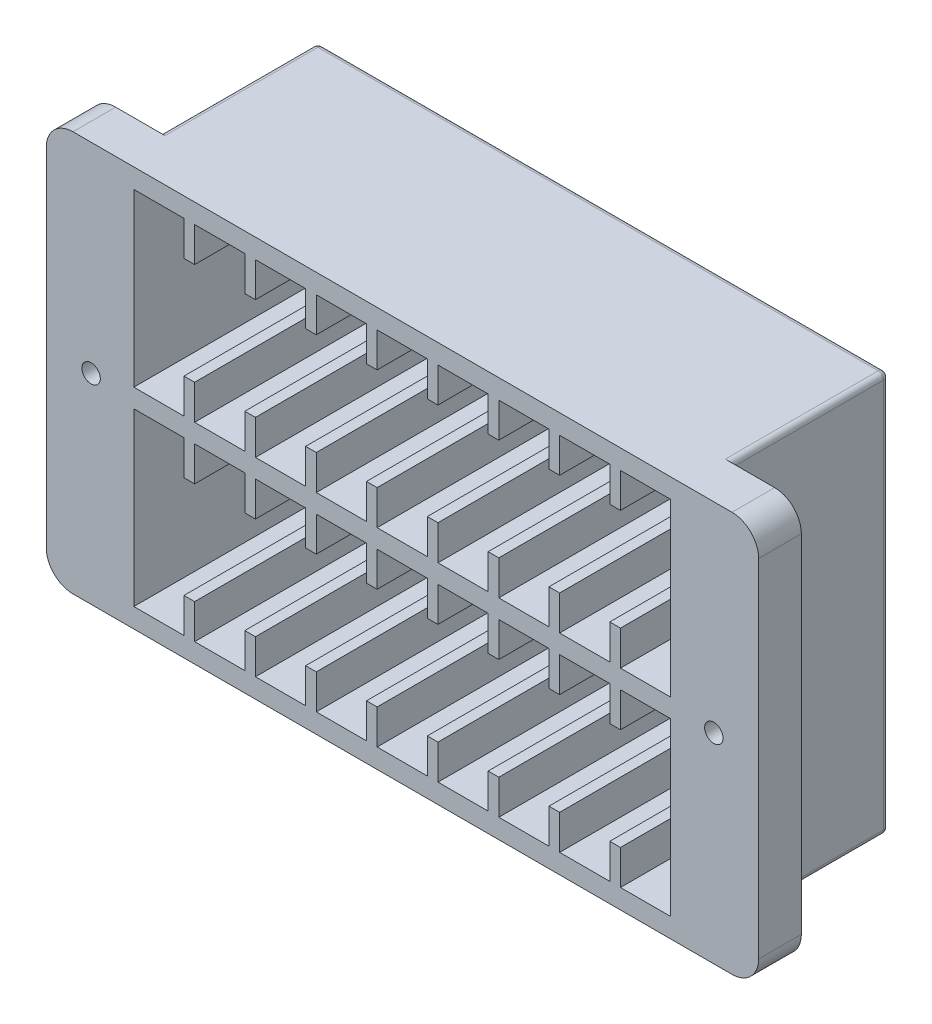
SolidWorks part; units mm, degrees
ref_plane "Front Plane" through (0, 0, 0) normal (0, 0, 1) x (1, 0, 0)
ref_plane "Top Plane" through (0, 0, 0) normal (0, 1, 0) x (1, 0, 0)
ref_plane "Right Plane" through (0, 0, 0) normal (1, 0, 0) x (0, 0, -1)
sketch "Sketch1" plane through (0, 0, 0) normal (0, 0, 1) x (1, 0, 0)
  line L0 (58.35, 0) -> (-58.35, 0) construction
  line L1 (66.75, -37.5) -> (-66.75, -37.5)
  line L2 (66.75, -37.5) -> (66.75, 37.5)
  line L3 (66.75, 37.5) -> (-66.75, 37.5)
  line L4 (-66.75, -37.5) -> (-66.75, 37.5)
  line L5 (66.75, -37.5) -> (-66.75, 37.5) construction
  line L6 (66.75, 37.5) -> (-66.75, -37.5) construction
  line L7 (-58.35, -1.725) -> (-58.35, 1.725) construction
  circle A0 centre (-58.35, 0) radius 1.725
  circle A1 centre (58.35, 0) radius 1.725
  point P0 (0, 0)
  point P9 (0, 0)
  point P24 (-58.35, 0)
  dimension "D4" = 3.45
  dimension "D1" = 133.5
  dimension "D2" = 75
  dimension "D3" = 116.7
extrude "Boss-Extrude1" add sketch "Sketch1" along normal blind 8
sketch "Sketch2" plane through (0, 0, 0) normal (0, 0, -1) x (-1, 0, 0)
  line L0 (-66.75, 37.5) -> (66.75, 37.5) construction
  line L1 (53.5, -37.5) -> (-53.5, -37.5)
  line L2 (53.5, -37.5) -> (53.5, 37.5)
  line L3 (53.5, 37.5) -> (-53.5, 37.5)
  line L4 (-53.5, -37.5) -> (-53.5, 37.5)
  line L5 (53.5, -37.5) -> (-53.5, 37.5) construction
  line L6 (53.5, 37.5) -> (-53.5, -37.5) construction
  point P0 (0, 0)
  dimension "D1" = 107
extrude "Boss-Extrude2" add sketch "Sketch2" along normal blind 29.65
sketch "Sketch3" plane through (0, 0, 8) normal (0, 0, 1) x (1, 0, 0)
  line L0 (0, -1.75) -> (0, 1.75) construction
  line L6 (48.4799, 33.85) -> (40.85, 33.85)
  line L19 (50.35, 0) -> (-50.35, 0) construction
  line L20 (-38.95, 33.85) -> (-38.95, 27.35)
  line L21 (-50.35, 33.85) -> (-40.95, 33.85)
  line L22 (-50.35, 33.85) -> (-50.35, 1.75)
  line L24 (-40.95, 33.85) -> (-40.95, 27.35)
  line L25 (-38.95, 33.85) -> (-29.55, 33.85)
  line L26 (-29.55, 33.85) -> (-29.55, 27.35)
  line L40 (-27.55, 33.85) -> (-27.55, 27.35)
  line L41 (-27.55, 33.85) -> (-18.15, 33.85)
  line L75 (-18.15, 33.85) -> (-18.15, 27.35)
  line L77 (-16.15, 33.85) -> (-16.15, 27.35)
  line L93 (-16.15, 33.85) -> (-6.75, 33.85)
  line L94 (-6.75, 33.85) -> (-6.75, 27.35)
  line L96 (-4.75, 33.85) -> (-4.75, 27.35)
  line L98 (-4.75, 33.85) -> (4.65, 33.85)
  line L99 (4.65, 33.85) -> (4.65, 27.35)
  line L101 (6.65, 33.85) -> (6.65, 27.35)
  line L102 (6.65, 33.85) -> (16.05, 33.85)
  line L103 (16.05, 33.85) -> (16.05, 27.35)
  line L105 (18.05, 33.85) -> (18.05, 27.35)
  line L106 (18.05, 33.85) -> (27.45, 33.85)
  line L107 (27.45, 33.85) -> (27.45, 27.35)
  line L109 (29.45, 33.85) -> (29.45, 27.35)
  line L110 (29.45, 33.85) -> (38.85, 33.85)
  line L111 (38.85, 33.85) -> (38.85, 27.35)
  line L113 (40.85, 33.85) -> (40.85, 27.35)
  line L114 (40.85, 33.85) -> (50.25, 33.85)
  line L115 (50.25, 33.85) -> (50.25, 1.75)
  line L118 (2.9667, -1.75) -> (-5.3771, 1.75) construction
  line L119 (3.1755, 1.75) -> (-3.1755, -1.75) construction
  line L155 (-40.95, 27.35) -> (-38.95, 27.35)
  line L165 (-50.35, 1.75) -> (-50.35, 33.85)
  line L166 (-29.55, 27.35) -> (-27.55, 27.35)
  line L167 (-18.15, 27.35) -> (-16.15, 27.35)
  line L168 (-6.75, 27.35) -> (-4.75, 27.35)
  line L169 (4.65, 27.35) -> (6.65, 27.35)
  line L170 (16.05, 27.35) -> (18.05, 27.35)
  line L171 (27.45, 27.35) -> (29.45, 27.35)
  line L173 (38.85, 27.35) -> (40.85, 27.35)
  line L174 (-50.35, 1.75) -> (50.25, 1.75)
  line L175 (-50.35, -1.75) -> (50.25, -1.75)
  line L176 (-40.95, 33.85) -> (-50.35, 33.85)
  line L177 (-29.55, 33.85) -> (-38.95, 33.85)
  line L178 (-18.15, 33.85) -> (-27.55, 33.85)
  line L179 (-6.75, 33.85) -> (-16.15, 33.85)
  line L180 (4.65, 33.85) -> (-4.75, 33.85)
  line L181 (16.05, 33.85) -> (6.65, 33.85)
  line L182 (27.45, 33.85) -> (18.05, 33.85)
  line L183 (38.85, 33.85) -> (29.45, 33.85)
  point P0 (0, 0)
  point P2 (0, 0)
  point P10 (0, 0)
  point P11 (0, 0)
  point P14 (0, 0)
  point P42 (0, 0)
  point P45 (0, 0)
  dimension "D2" = 32.1
  dimension "D3" = 9.4
  dimension "D4" = 2
  dimension "D5" = 9
  dimension "D7" = 6.5
  dimension "D6" = 50.35
  dimension "D15" = 3.5
  dimension "D18" = 100.7
extrude "Cut-Extrude1" cut sketch "Sketch3" against normal blind 32.65 contours L22 L174 L115 L6 L113 L173 L111 L110 L109 L171 L107 L106 L105 L170 L103 L102 L101 L169 L99 L98 L96 L168 L94 L93 L77 L167 L75 L41 L40 L166 L26 L25 L20 L155 L24 L21
mirror "Mirror1" about plane through (0, 0, 0) normal (0, 1, 0) of "Cut-Extrude1"
sketch "Sketch4" plane through (0, 0, 8) normal (0, 0, 1) x (1, 0, 0)
  line L0 (-50.35, 1.75) -> (50.25, 1.75) construction
  line L1 (-40.95, 1.75) -> (-38.95, 1.75)
  line L2 (-40.95, 1.75) -> (-40.95, 8.25)
  line L3 (-40.95, 8.25) -> (-38.95, 8.25)
  line L4 (-38.95, 1.75) -> (-38.95, 8.25)
  line L5 (-40.95, 33.85) -> (-40.95, 27.35) construction
  line L6 (-29.55, 1.75) -> (-29.55, 8.25)
  line L7 (-29.55, 1.75) -> (-27.55, 1.75)
  line L8 (-27.55, 1.75) -> (-27.55, 8.25)
  line L9 (-29.55, 8.25) -> (-27.55, 8.25)
  line L10 (-18.15, 1.75) -> (-18.15, 8.25)
  line L11 (-18.15, 1.75) -> (-16.15, 1.75)
  line L12 (-16.15, 1.75) -> (-16.15, 8.25)
  line L13 (-18.15, 8.25) -> (-16.15, 8.25)
  line L14 (-6.75, 1.75) -> (-6.75, 8.25)
  line L15 (-6.75, 1.75) -> (-4.75, 1.75)
  line L16 (-4.75, 1.75) -> (-4.75, 8.25)
  line L17 (-6.75, 8.25) -> (-4.75, 8.25)
  line L18 (4.65, 1.75) -> (4.65, 8.25)
  line L19 (4.65, 1.75) -> (6.65, 1.75)
  line L20 (6.65, 1.75) -> (6.65, 8.25)
  line L21 (4.65, 8.25) -> (6.65, 8.25)
  line L22 (16.05, 1.75) -> (16.05, 8.25)
  line L23 (16.05, 1.75) -> (18.05, 1.75)
  line L24 (18.05, 1.75) -> (18.05, 8.25)
  line L25 (16.05, 8.25) -> (18.05, 8.25)
  line L26 (27.45, 1.75) -> (27.45, 8.25)
  line L27 (27.45, 1.75) -> (29.45, 1.75)
  line L28 (29.45, 1.75) -> (29.45, 8.25)
  line L29 (27.45, 8.25) -> (29.45, 8.25)
  line L30 (38.85, 1.75) -> (38.85, 8.25)
  line L31 (38.85, 1.75) -> (40.85, 1.75)
  line L32 (40.85, 1.75) -> (40.85, 8.25)
  line L33 (38.85, 8.25) -> (40.85, 8.25)
  dimension "D1" = 2
  dimension "D2" = 6.5
  dimension "D4" = 9.4
  dimension "D3" = 8
extrude "Boss-Extrude3" add sketch "Sketch4" against normal up to surface (32.65 mm away) up to face at (-0.05, 29.1778, -24.65)
mirror "Mirror2" about plane through (0, 0, 0) normal (0, 1, 0) of "Boss-Extrude3"
sketch "Sketch5" plane through (0, 0, 8) normal (0, 0, 1) x (1, 0, 0)
  line L0 (-40.95, -8.25) -> (-40.95, -1.75) construction
  line L1 (-50.35, -1.75) -> (-40.95, -1.75)
  line L2 (-50.35, -1.75) -> (-50.35, -1.25)
  line L3 (-50.35, -1.25) -> (-40.95, -1.25)
  line L4 (-40.95, -1.75) -> (-40.95, -1.25)
  line L5 (-38.95, -1.75) -> (-38.95, -1.25)
  line L6 (-38.95, -1.75) -> (-29.55, -1.75)
  line L7 (-29.55, -1.75) -> (-29.55, -1.25)
  line L8 (-38.95, -1.25) -> (-29.55, -1.25)
  line L9 (-27.55, -1.75) -> (-27.55, -1.25)
  line L10 (-27.55, -1.75) -> (-18.15, -1.75)
  line L11 (-18.15, -1.75) -> (-18.15, -1.25)
  line L12 (-27.55, -1.25) -> (-18.15, -1.25)
  line L13 (-16.15, -1.75) -> (-16.15, -1.25)
  line L14 (-16.15, -1.75) -> (-6.75, -1.75)
  line L15 (-6.75, -1.75) -> (-6.75, -1.25)
  line L16 (-16.15, -1.25) -> (-6.75, -1.25)
  line L17 (-4.75, -1.75) -> (-4.75, -1.25)
  line L18 (-4.75, -1.75) -> (4.65, -1.75)
  line L19 (4.65, -1.75) -> (4.65, -1.25)
  line L20 (-4.75, -1.25) -> (4.65, -1.25)
  line L21 (6.65, -1.75) -> (6.65, -1.25)
  line L22 (6.65, -1.75) -> (16.05, -1.75)
  line L23 (16.05, -1.75) -> (16.05, -1.25)
  line L24 (6.65, -1.25) -> (16.05, -1.25)
  line L25 (18.05, -1.75) -> (18.05, -1.25)
  line L26 (18.05, -1.75) -> (27.45, -1.75)
  line L27 (27.45, -1.75) -> (27.45, -1.25)
  line L28 (18.05, -1.25) -> (27.45, -1.25)
  line L29 (29.45, -1.75) -> (29.45, -1.25)
  line L30 (29.45, -1.75) -> (38.85, -1.75)
  line L31 (38.85, -1.75) -> (38.85, -1.25)
  line L32 (29.45, -1.25) -> (38.85, -1.25)
  line L33 (40.85, -1.75) -> (40.85, -1.25)
  line L34 (40.85, -1.75) -> (50.25, -1.75)
  line L35 (50.25, -1.75) -> (50.25, -1.25)
  line L36 (40.85, -1.25) -> (50.25, -1.25)
  dimension "D1" = 0.5
  dimension "D3" = 2
  dimension "D2" = 9
extrude "Cut-Extrude2" [suppressed] cut sketch "Sketch5" against normal up to surface (32.5 mm away)
fillet "Fillet1" radius 5 4 edges at (-66.75, 37.5, 4) (66.75, 37.5, 4) (66.75, -37.5, 4) (-66.75, -37.5, 4)
fillet "Fillet3" [suppressed] radius 1
fillet "Fillet4" radius 1 8 edges at (0, 37.5, -29.65) (-53.5, 0, -29.65) (0, -37.5, -29.65) (53.5, 0, -29.65) (53.5, -37.5, -14.825) (53.5, 37.5, -14.825) (-53.5, 37.5, -14.825) (-53.5, -37.5, -14.825)
